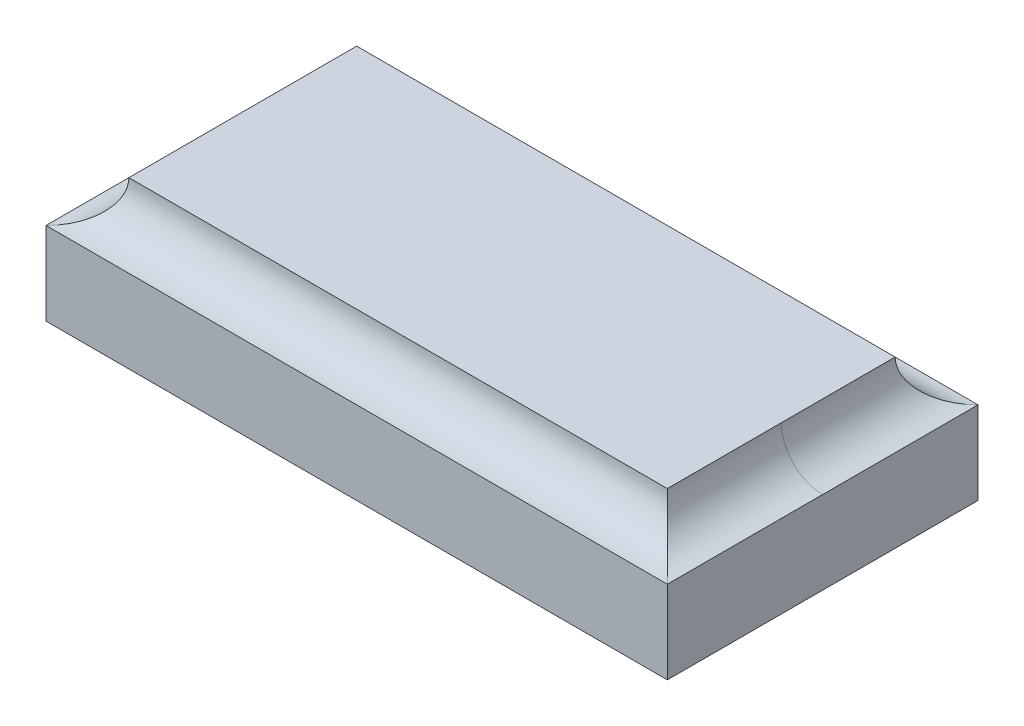
SolidWorks part; units mm, degrees
ref_plane "Front Plane" through (0, 0, 0) normal (0, 0, 1) x (1, 0, 0)
ref_plane "Top Plane" through (0, 0, 0) normal (0, 1, 0) x (1, 0, 0)
ref_plane "Right Plane" through (0, 0, 0) normal (1, 0, 0) x (0, 0, -1)
sketch "Sketch2" plane through (0, 0, 0) normal (0, 1, 0) x (1, 0, 0)
  line L1 (150, 75) -> (-150, 75)
  line L2 (150, 75) -> (150, -75)
  line L3 (150, -75) -> (-150, -75)
  line L4 (-150, 75) -> (-150, -75)
  line L5 (150, 75) -> (-150, -75) construction
  line L6 (150, -75) -> (-150, 75) construction
  point P0 (0, 0)
  dimension "D1" = 150
  dimension "D2" = 300
extrude "Boss-Extrude1" add sketch "Sketch2" along normal blind 60
sketch "Sketch3" plane through (0, 0, 0) normal (0, 0, 1) x (1, 0, 0)
  circle A0 centre (150, 60) radius 20
  dimension "D1" = 40
sketch "Sketch4" plane through (0, 60, 0) normal (0, 1, 0) x (1, 0, 0)
  line L4 (-150, 75) -> (-150, -75)
  line L5 (-150, -75) -> (150, -75)
  line L6 (150, -75) -> (150, 75)
  line L7 (150, 75) -> (-150, 75)
  line L8 (-150, 75) -> (-150, -75)
  line L9 (-150, -75) -> (150, -75)
  line L10 (150, -75) -> (150, 75)
  line L11 (150, 75) -> (-150, 75)
  dimension "D1" = 0
sweep "Cut-Sweep3" cut profiles "Sketch3" path "Sketch4"
